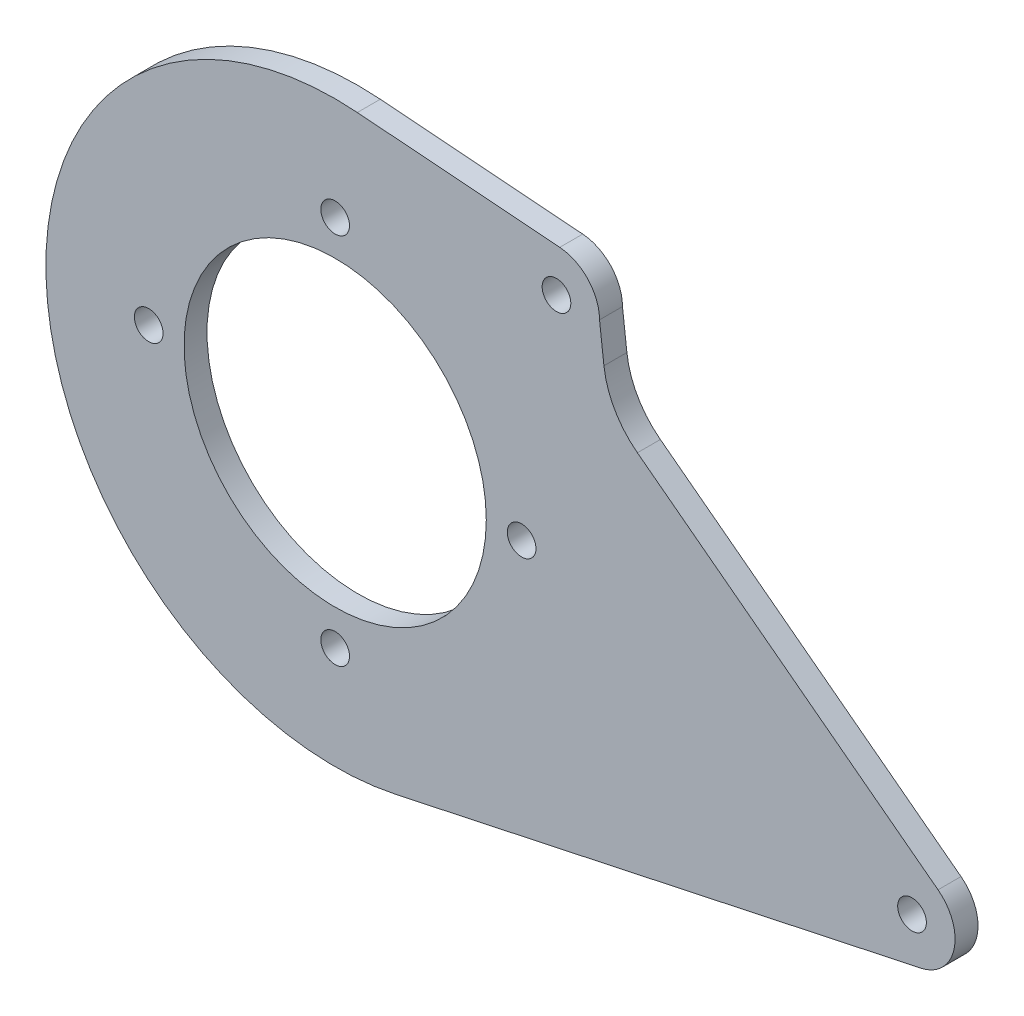
SolidWorks part; units mm, degrees
ref_plane "Front Plane" through (0, 0, 0) normal (0, 0, 1) x (1, 0, 0)
ref_plane "Top Plane" through (0, 0, 0) normal (0, 1, 0) x (1, 0, 0)
ref_plane "Right Plane" through (0, 0, 0) normal (1, 0, 0) x (0, 0, -1)
sketch "Sketch2" plane through (0, 0, 0) normal (0, 0, 1) x (1, 0, 0)
  line L3 (26.7128, -125.1816) -> (259.2067, -75.5692)
  line L4 (-465.3966, 682.9035) -> (262.1484, -78.6484) construction
  line L5 (9.8051, 127.6239) -> (99.3807, 120.742)
  line L6 (133.7246, 59.1995) -> (266.7532, -41.763)
  line L8 (118.9161, 85.1223) -> (116.9714, 101.748)
  circle A1 centre (0, 0) radius 66.87
  arc A2 (65.6, 0) -> (-65.6, 0) centre (0, 0) ccw construction
  circle A3 centre (0, 82.5) radius 6.35
  circle A4 centre (-82.5, 0) radius 6.35
  circle A5 centre (0, -82.5) radius 6.35
  circle A6 centre (82.5, 0) radius 6.35
  arc A10 (9.8051, 127.6239) -> (26.7128, -125.1816) centre (0, 0) ccw
  circle A11 centre (255.2365, -56.9375) radius 6.35
  arc A12 (259.2067, -75.5692) -> (266.7532, -41.763) centre (255.2365, -56.9375) ccw
  circle A13 centre (97.9214, 101.748) radius 6.35
  arc A14 (116.9714, 101.748) -> (99.3807, 120.742) centre (97.9214, 101.748) ccw
  arc A16 (17.4142, -126.8099) -> (48.3238, -118.5277) centre (0, 0) ccw construction
  arc A17 (133.7246, 59.1995) -> (118.9161, 85.1223) centre (156.7581, 89.5486) cw
  point P0 (0, 0)
  dimension "D3" = 1.27
  dimension "D4" = 12.7
  dimension "D5" = 12.7
  dimension "D1" = 12.7
  dimension "D2" = 12.7
  dimension "D6" = 38.1
extrude "Boss-Extrude1" add sketch "Sketch2" along normal blind 10.16
